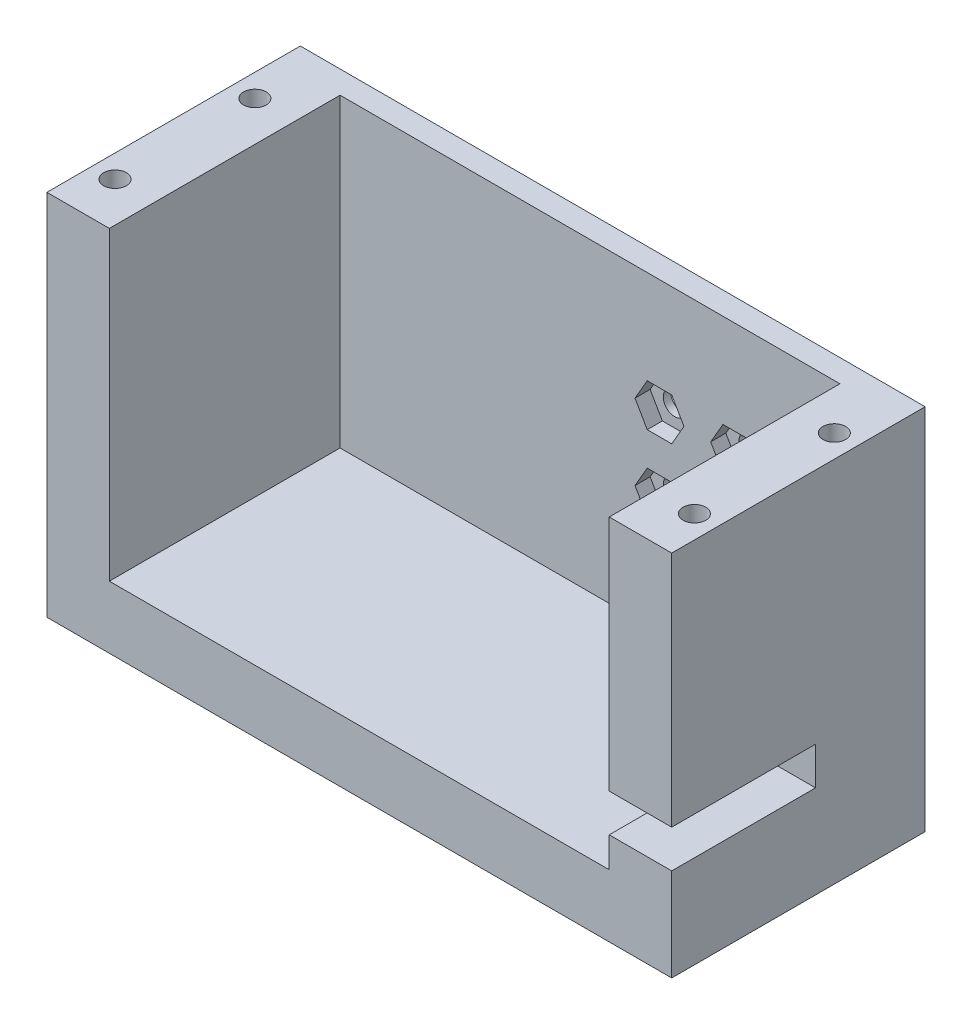
SolidWorks part; units mm, degrees
material "6061 합금"
ref_plane "정면" through (0, 0, 0) normal (0, 0, 1) x (1, 0, 0)
ref_plane "윗면" through (0, 0, 0) normal (0, 1, 0) x (1, 0, 0)
ref_plane "우측면" through (0, 0, 0) normal (1, 0, 0) x (0, 0, -1)
sketch "스케치3" plane through (0, 0, 0) normal (0, 0, 1) x (1, 0, 0)
  line L0 (21517.5223, 8422.8529) -> (21525.7773, 8422.8529)
  line L1 (21600.0723, 8374.2325) -> (21517.5223, 8374.2325)
  line L2 (21600.0723, 8374.2325) -> (21600.0723, 8422.8529)
  line L3 (21525.7773, 8422.8529) -> (21525.7773, 8382.4875)
  line L4 (21517.5223, 8374.2325) -> (21517.5223, 8422.8529)
  line L5 (21525.7773, 8382.4875) -> (21591.8173, 8382.4875)
  line L6 (21591.8173, 8382.4875) -> (21591.8173, 8422.8529)
  line L7 (21591.8173, 8422.8529) -> (21600.0723, 8422.8529)
  dimension "D1" = 8.255
  dimension "D2" = 8.255
  dimension "D3" = 48.6204
  dimension "D4" = 40.3654
  dimension "D5" = 40.3654
  dimension "D6" = 82.55
extrude "보스-돌출1" add sketch "스케치3" along normal blind 30.48
ref_plane "평면1" through (0, 8374.2325, 0) normal (0, -1, 0) x (-1, 0, 0)
sketch "스케치4" plane through (0, 8374.2325, 0) normal (0, -1, 0) x (-1, 0, 0)
  line L0 (-21517.5223, -30.48) -> (-21517.5223, 0) construction
  line L1 (-21517.5223, -30.48) -> (-21600.0723, -30.48) construction
  circle A0 centre (-21576.7175, -15.24) radius 3.302
  point P0 (-21576.7175, -15.24)
  dimension "D3" = 6.604
  dimension "D1" = 59.1951
  dimension "D2" = 15.24
extrude "보스-돌출2" add sketch "스케치4" along normal blind 6.1246
ref_plane "평면2" through (0, 0, 0) normal (0, 0, -1) x (-1, 0, 0)
sketch "스케치5" plane through (0, 0, 0) normal (0, 0, -1) x (-1, 0, 0)
  line L0 (-16.764, 8374.2325) -> (16.764, 8374.2325) construction
  line L1 (-21600.0723, 8422.8529) -> (-21517.5223, 8422.8529)
  line L2 (-21600.0723, 8422.8529) -> (-21600.0723, 8374.2325)
  line L3 (-21600.0723, 8374.2325) -> (-21517.5223, 8374.2325)
  line L4 (-21517.5223, 8422.8529) -> (-21517.5223, 8374.2325)
  line L5 (-21517.5223, 8422.8529) -> (-21517.5223, 8374.2325) construction
extrude "보스-돌출3" add sketch "스케치5" along normal blind 3
ref_plane "평면3" through (0, 0, 0) normal (0, 0, 1) x (1, 0, 0)
sketch "스케치6" plane through (0, 0, 0) normal (0, 0, 1) x (1, 0, 0)
  line L1 (21525.7773, 8422.8529) -> (21525.7773, 8382.4875) construction
  line L2 (21591.8173, 8382.4875) -> (21525.7773, 8382.4875) construction
  line L3 (21517.5223, 8422.8529) -> (21517.5223, 8374.2325) construction
  line L4 (21517.5223, 8402.6725) -> (21600.0723, 8402.6725) construction
  line L5 (21600.0723, 8374.2325) -> (21600.0723, 8422.8529) construction
  circle A1 centre (21577.9766, 8407.6725) radius 1.5
  circle A3 centre (21567.9766, 8407.6725) radius 1.5
  circle A4 centre (21567.9766, 8397.6725) radius 1.5
  circle A6 centre (21577.9766, 8397.6725) radius 1.5
  dimension "D10" = 3
  dimension "D11" = 3
  dimension "D1" = 20.185
  dimension "D2" = 40.3654
  dimension "D3" = 5
  dimension "D6" = 10
  dimension "D7" = 5
extrude "컷-돌출1" cut sketch "스케치6" against normal blind 3
ref_plane "평면4" through (0, 0, 0) normal (0, 0, 1) x (1, 0, 0)
sketch "스케치7" plane through (0, 0, 0) normal (0, 0, 1) x (1, 0, 0)
  line L0 (21569.5932, 8410.4725) -> (21566.36, 8410.4725)
  line L1 (21566.36, 8410.4725) -> (21564.7434, 8407.6725)
  line L2 (21564.7434, 8407.6725) -> (21566.36, 8404.8725)
  line L3 (21566.36, 8404.8725) -> (21569.5932, 8404.8725)
  line L4 (21569.5932, 8404.8725) -> (21571.2097, 8407.6725)
  line L5 (21571.2097, 8407.6725) -> (21569.5932, 8410.4725)
  line L6 (21566.36, 8410.4725) -> (21569.5932, 8404.8725) construction
  line L7 (21569.5932, 8410.4725) -> (21566.36, 8404.8725) construction
  line L8 (21564.7434, 8407.6725) -> (21571.2097, 8407.6725) construction
  line L9 (21569.5932, 8400.4725) -> (21566.36, 8400.4725)
  line L10 (21566.36, 8400.4725) -> (21564.7434, 8397.6725)
  line L11 (21564.7434, 8397.6725) -> (21566.36, 8394.8725)
  line L12 (21566.36, 8394.8725) -> (21569.5932, 8394.8725)
  line L13 (21569.5932, 8394.8725) -> (21571.2097, 8397.6725)
  line L14 (21571.2097, 8397.6725) -> (21569.5932, 8400.4725)
  line L15 (21566.36, 8400.4725) -> (21569.5932, 8394.8725) construction
  line L16 (21569.5932, 8400.4725) -> (21566.36, 8394.8725) construction
  line L17 (21564.7434, 8397.6725) -> (21571.2097, 8397.6725) construction
  line L18 (21579.5932, 8400.4725) -> (21576.36, 8400.4725)
  line L19 (21576.36, 8400.4725) -> (21574.7434, 8397.6725)
  line L20 (21574.7434, 8397.6725) -> (21576.36, 8394.8725)
  line L21 (21576.36, 8394.8725) -> (21579.5932, 8394.8725)
  line L22 (21579.5932, 8394.8725) -> (21581.2097, 8397.6725)
  line L23 (21581.2097, 8397.6725) -> (21579.5932, 8400.4725)
  line L24 (21576.36, 8400.4725) -> (21579.5932, 8394.8725) construction
  line L25 (21579.5932, 8400.4725) -> (21576.36, 8394.8725) construction
  line L26 (21574.7434, 8397.6725) -> (21581.2097, 8397.6725) construction
  line L27 (21579.5932, 8410.4725) -> (21576.36, 8410.4725)
  line L28 (21576.36, 8410.4725) -> (21574.7434, 8407.6725)
  line L29 (21574.7434, 8407.6725) -> (21576.36, 8404.8725)
  line L30 (21576.36, 8404.8725) -> (21579.5932, 8404.8725)
  line L31 (21579.5932, 8404.8725) -> (21581.2097, 8407.6725)
  line L32 (21581.2097, 8407.6725) -> (21579.5932, 8410.4725)
  line L33 (21576.36, 8410.4725) -> (21579.5932, 8404.8725) construction
  line L34 (21579.5932, 8410.4725) -> (21576.36, 8404.8725) construction
  line L35 (21574.7434, 8407.6725) -> (21581.2097, 8407.6725) construction
  circle A0 centre (21567.9766, 8407.6725) radius 1.5
  circle A1 centre (21567.9766, 8397.6725) radius 1.5
  circle A2 centre (21577.9766, 8397.6725) radius 1.5
  circle A3 centre (21577.9766, 8407.6725) radius 1.5
  dimension "D1" = 3.2332
  dimension "D2" = 3.2332
  dimension "D3" = 3.2332
  dimension "D4" = 3.2332
  dimension "D5" = 3.2332
  dimension "D6" = 3.2332
  dimension "D7" = 3.2332
  dimension "D8" = 3.2332
  dimension "D9" = 3.2332
  dimension "D10" = 3.2332
  dimension "D11" = 3.2332
  dimension "D12" = 3.2332
  dimension "D13" = 3.2332
  dimension "D14" = 3.2332
  dimension "D15" = 3.2332
  dimension "D16" = 3.2332
  dimension "D17" = 3.2332
  dimension "D18" = 3.2332
  dimension "D19" = 3.2332
  dimension "D20" = 3.2332
  dimension "D21" = 3.2332
  dimension "D22" = 3.2332
  dimension "D23" = 3.2332
  dimension "D24" = 3.2332
extrude "컷-돌출2" cut sketch "스케치7" against normal blind 2
ref_plane "평면5" through (0, 8422.8529, 0) normal (0, 1, 0) x (1, 0, 0)
sketch "스케치8" plane through (0, 8422.8529, 0) normal (0, 1, 0) x (1, 0, 0)
  line L0 (21600.0723, -30.48) -> (21591.8173, -30.48) construction
  line L1 (-30.1098, 0) -> (30.1098, 0) construction
  line L2 (21600.0723, -30.48) -> (21600.0723, 3) construction
  line L3 (21558.7973, 3) -> (21558.7973, -30.48) construction
  line L4 (21517.5223, 3) -> (21600.0723, 3) construction
  line L5 (21591.8173, -30.48) -> (21525.7773, -30.48) construction
  circle A0 centre (21597.0723, -6) radius 1.5
  circle A1 centre (21597.0723, -24.48) radius 1.5
  circle A2 centre (21520.5223, -24.48) radius 1.5
  circle A3 centre (21520.5223, -6) radius 1.5
  point P0 (21597.0723, -24.48)
  point P1 (21597.0723, -6)
  dimension "D5" = 3
  dimension "D6" = 3
  dimension "D1" = 6
  dimension "D2" = 6
  dimension "D3" = 3
  dimension "D4" = 3
extrude "컷-돌출3" cut sketch "스케치8" against normal blind 10
ref_plane "평면6" through (0, 0, 30.48) normal (0, 0, 1) x (1, 0, 0)
sketch "스케치9" plane through (0, 0, 30.48) normal (0, 0, 1) x (1, 0, 0)
  line L1 (21591.8173, 8422.8529) -> (21591.8173, 8382.4875) construction
  line L2 (21591.8173, 8386.4875) -> (21600.0723, 8386.4875)
  line L3 (21591.8173, 8386.4875) -> (21591.8173, 8391.4875)
  line L4 (21591.8173, 8391.4875) -> (21600.0723, 8391.4875)
  line L10 (21600.0723, 8386.4875) -> (21600.0723, 8391.4875)
  line L11 (21600.0723, 8374.2325) -> (21600.0723, 8422.8529) construction
  line L12 (21591.8173, 8382.4875) -> (21525.7773, 8382.4875) construction
  dimension "D2" = 5
  dimension "D3" = 4
extrude "컷-돌출4" cut sketch "스케치9" against normal blind 19
ref_plane "평면7" through (0, 0, 30.48) normal (0, 0, 1) x (1, 0, 0)
